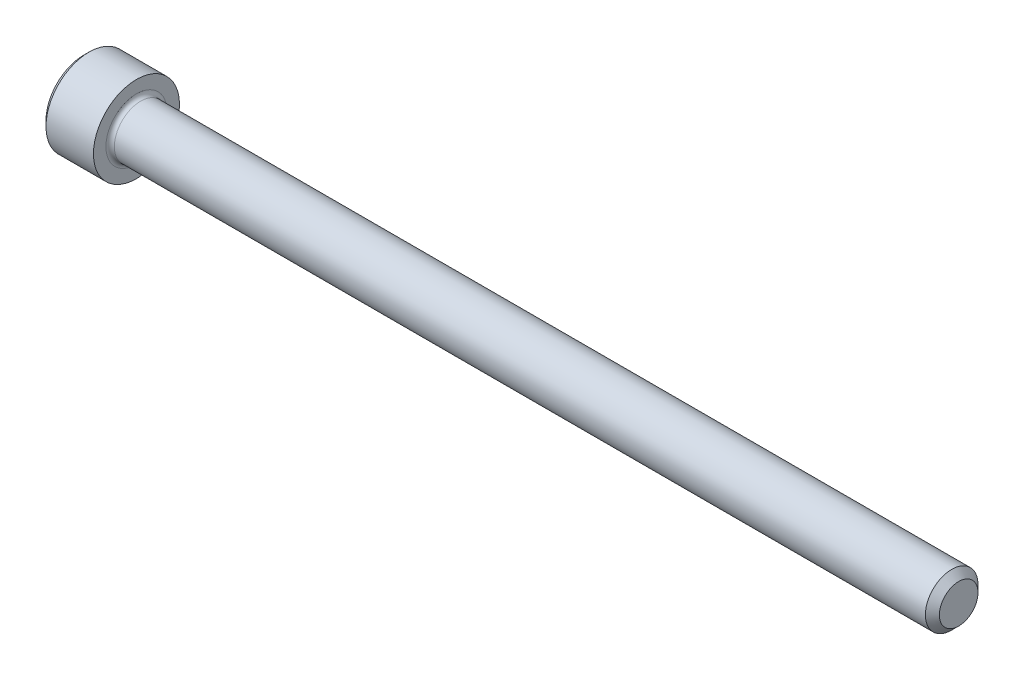
SolidWorks part; units mm, degrees
ref_plane "Plane1" through (0, 0, 0) normal (0, 0, 1) x (1, 0, 0)
ref_plane "Plane2" through (0, 0, 0) normal (0, 1, 0) x (1, 0, 0)
ref_plane "Plane3" through (0, 0, 0) normal (1, 0, 0) x (0, 0, -1)
sketch "BodySke" plane through (0, 0, 0) normal (0, 0, 1) x (1, 0, 0)
  line L0 (0, 0) -> (0, 2.0447)
  line L1 (0.2794, 2.3241) -> (2.8448, 2.3241)
  line L2 (2.8448, 2.3241) -> (2.8448, 1.4224)
  line L3 (2.8448, 1.4224) -> (46.9163, 1.4224)
  line L4 (47.2948, 1.0439) -> (47.2948, 0)
  line L5 (47.2948, 0) -> (0, 0)
  line L6 (-31.75, 0) -> (127, 0) construction
  line L7 (0, 2.0447) -> (0.2794, 2.3241)
  line L8 (47.2948, 1.0439) -> (46.9163, 1.4224)
  line L9 (0, -2.0447) -> (0.2794, -2.3241) construction
  line L10 (47.2948, -1.0439) -> (46.9163, -1.4224) construction
  line L11 (3.4798, 9.525) -> (3.4798, 3.175) construction
  line L12 (21.8948, 9.525) -> (21.8948, 3.175) construction
  line L13 (9.1948, 9.525) -> (9.1948, 3.175) construction
  dimension "Diameter" = 2.8448
  dimension "Head_ht" = 2.8448
  dimension "Length" = 44.45
  dimension "Body_ch_ang" = 45
  dimension "Head_dia" = 4.6482
  dimension "Head_ch_ang" = 45
  dimension "Head_side_ht" = 2.5654
  dimension "Minor_dia" = 2.0879
  dimension "Advance" = 0.635
  dimension "Thread_nom" = 25.4
  dimension "Thread_length" = 38.1
revolve "Base-Revolve" add sketch "BodySke"
cosmetic thread "ThreadCosmetic" [suppressed]
fillet "Fillet1" radius 0.2286 1 edges at (2.8448, 0, 1.4224)
sketch "Sketch2" plane through (0, 0, 0) normal (0, 0, 1) x (1, 0, 0)
  line L0 (0, 1.1938) -> (1.2954, 1.1938)
  line L1 (1.2954, 1.1938) -> (1.9846, 0)
  line L2 (-31.75, 0) -> (127, 0) construction
  line L3 (1.9846, 0) -> (0, 0)
  line L4 (0, 0) -> (0, 1.1938)
  line L5 (0, 2.0447) -> (0, -2.0447) construction
  line L6 (0, 0) -> (47.625, 0) construction
  line L7 (2.8448, -2.3241) -> (2.8448, 2.3241) construction
  dimension "D1" = 1.1938
  dimension "D2" = 60
  dimension "Wall_thickness" = 1.5494
revolve "Hex-PreBroach" cut sketch "Sketch2" angle 360 about L6
sketch "Sketch3" plane through (0, 0, 0) normal (-1, 0, 0) x (0, 0.5, 0.866)
  line L0 (0.6892, 1.1938) -> (-0.6892, 1.1938)
  line L1 (-0.6892, 1.1938) -> (-1.3785, 0)
  line L2 (0.6892, 1.1938) -> (1.3785, 0)
  line L3 (0.6892, -1.1938) -> (1.3785, 0)
  line L4 (0.6892, -1.1938) -> (-0.6892, -1.1938)
  line L5 (-0.6892, -1.1938) -> (-1.3785, 0)
  dimension "D1" = 1.1938
  dimension "D2" = 1.1938
  dimension "Hex_size" = 2.3876
extrude "Hex" cut sketch "Sketch3" against normal blind 1.2954
sketch "Sketch4" plane through (0, 0, 0) normal (-1, 0, 0) x (0, 0, 1)
  line L0 (0, 0) -> (1.4605, 0)
  line L1 (0, 0) -> (6.1484, 3.5498) construction
  line L2 (0, 0) -> (0.7302, 1.2648)
  line L3 (1.2009, 0.3267) -> (1.3933, 0.4378)
  line L4 (0.8834, 0.8767) -> (1.0758, 0.9877)
  arc A0 (1.2009, 0.3267) -> (0.8834, 0.8767) centre (0, 0) ccw
  arc A1 (1.4605, 0) -> (1.3933, 0.4378) centre (0, 0) ccw
  arc A2 (0.7302, 1.2648) -> (1.0758, 0.9877) centre (0, 0) cw
  dimension "D1" = 30
  dimension "Spline_n_dim" = 2.4892
  dimension "Spline_m_dim" = 2.921
  dimension "D2" = 60
  dimension "D3" = 0.3175
  dimension "Spline_p_dim" = 0.635
extrude "Spline" [suppressed] cut sketch "Sketch4" against normal blind 1.2954
pattern_circular "CirPattern1" [suppressed] count 6 every 60
sketch "Sketch5" plane through (0, 0, 0) normal (0, 0, 1) x (1, 0, 0)
  line L0 (-31.75, 0) -> (127, 0) construction
  line L2 (0, 2.0447) -> (0, -2.0447) construction
  circle A0 centre (1.016, 0) radius 0.4445
  dimension "Drilled_hole_dia" = 0.889
  dimension "Drilled_hole_loc" = 1.016
extrude "Hole" [suppressed] cut sketch "Sketch5" against normal through all and the other way through all
pattern_circular "Drilled-4" [suppressed] count 2 every 60
pattern_circular "Drilled-6" [suppressed] count 3 every 60
sketch "ThdSchSke" plane through (0, 0, 0) normal (0, 0, 1) x (1, 0, 0)
  line L0 (21.8948, -1.0439) -> (21.6298, -1.4224)
  line L1 (21.8948, -1.0439) -> (22.1598, -1.4224)
  line L2 (22.1598, -1.4224) -> (22.1598, -1.778)
  line L3 (-3.175, 0) -> (5.1513, 0) construction
  line L5 (22.1598, -1.778) -> (21.6298, -1.778)
  line L6 (21.6298, -1.778) -> (21.6298, -1.4224)
  line L7 (0, 2.0447) -> (0, -2.0447) construction
  dimension "Thread_minor" = 2.0879
  dimension "Diameter" = 2.8448
  dimension "Start" = 21.8948
  dimension "SideAngle" = 55
  dimension "VeeAngle" = 70
  dimension "Overcut" = 3.556
revolve "ThreadSchematic" [suppressed] cut sketch "ThdSchSke" angle 360 about L3
pattern_linear "ThdSchPat" [suppressed]
equation "\"D2@Sketch3\" = \"Hex_size@Sketch3\" / 2"
equation "\"D1@Sketch3\" = \"Hex_size@Sketch3\" / 2"
equation "\"D1@Sketch2\" = \"Hex_size@Sketch3\" / 2"
equation "\"D3@Sketch4\" = \"Spline_p_dim@Sketch4\" / 2"
equation "\"Thread_minor@ThreadCosmetic\"  =  \"Minor_dia@BodySke\""
equation "\"D2@CirPattern1\" = 360 / \"Num_teeth@CirPattern1\""
equation "\"Wall_thickness@Sketch2\" = \"Head_ht@BodySke\" - \"Key_eng@Hex\""
equation "\"Thread_length@ThreadCosmetic\" = ((sgn( (\"Length@BodySke\" - \"Advance@BodySke\" ) - \"Thread_nom@BodySke\" )-1)*( (\"Length@BodySke\" - \"Advance@BodySke\" ) - \"Thread_nom@BodySke\" ))/-2+ \"Thread_nom@BodySke\""
equation "\"Thread_minor@ThdSchSke\" = \"Minor_dia@BodySke\""
equation "\"Diameter@ThdSchSke\" = \"Diameter@BodySke\""
equation "\"Overcut@ThdSchSke\" = \"Diameter@BodySke\" * 1.25"
equation "\"Start@ThdSchSke\" = \"Head_ht@BodySke\" + \"Length@BodySke\" - \"Thread_length@ThreadCosmetic\"  '---Non-countersunk---"
equation "\"Num_threads@ThdSchPat\" = int( \"Thread_length@ThreadCosmetic\" / \"Advance@BodySke\" + 0.999 )  + 1"
equation "\"Advance@ThdSchPat\" = \"Thread_length@ThreadCosmetic\" /  (\"Num_threads@ThdSchPat\" - 1) 'relax it"
equation "\"Num_threads@ThdSchPat\" = \"Num_threads@ThdSchPat\" - sgn( \"Num_threads@ThdSchPat\" - 1) '---chamfered tips only---"
